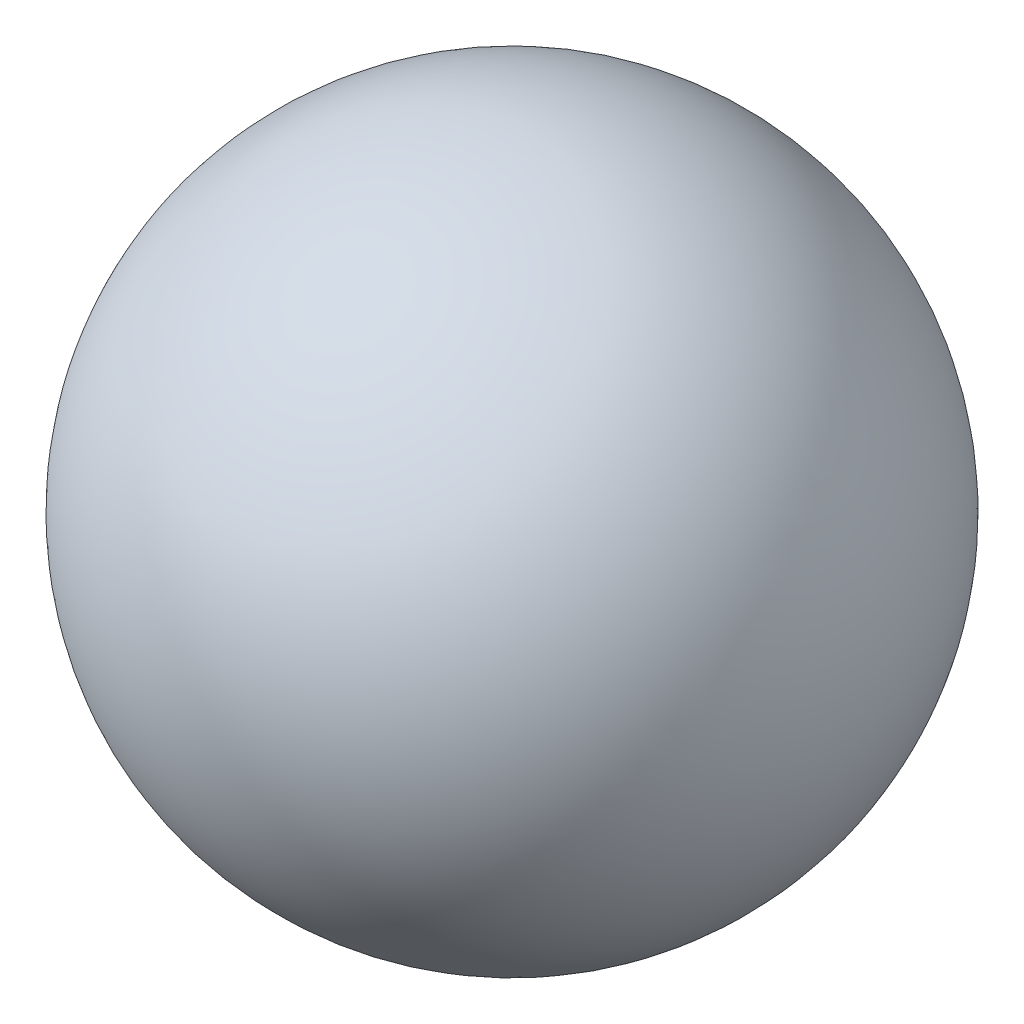
SolidWorks part; units mm, degrees
ref_plane "Front Plane" through (0, 0, 0) normal (0, 0, 1) x (1, 0, 0)
ref_plane "Top Plane" through (0, 0, 0) normal (0, 1, 0) x (1, 0, 0)
ref_plane "Right Plane" through (0, 0, 0) normal (1, 0, 0) x (0, 0, -1)
sketch "Sketch1" plane through (0, 0, 0) normal (0, 1, 0) x (1, 0, 0)
  line L0 (-1.5, 0) -> (1.5, 0)
  arc A0 (-1.5, 0) -> (1.5, 0) centre (0, 0) cw
  dimension "D1" = 3
revolve "Revolve1" add sketch "Sketch1" angle 360 about L0
